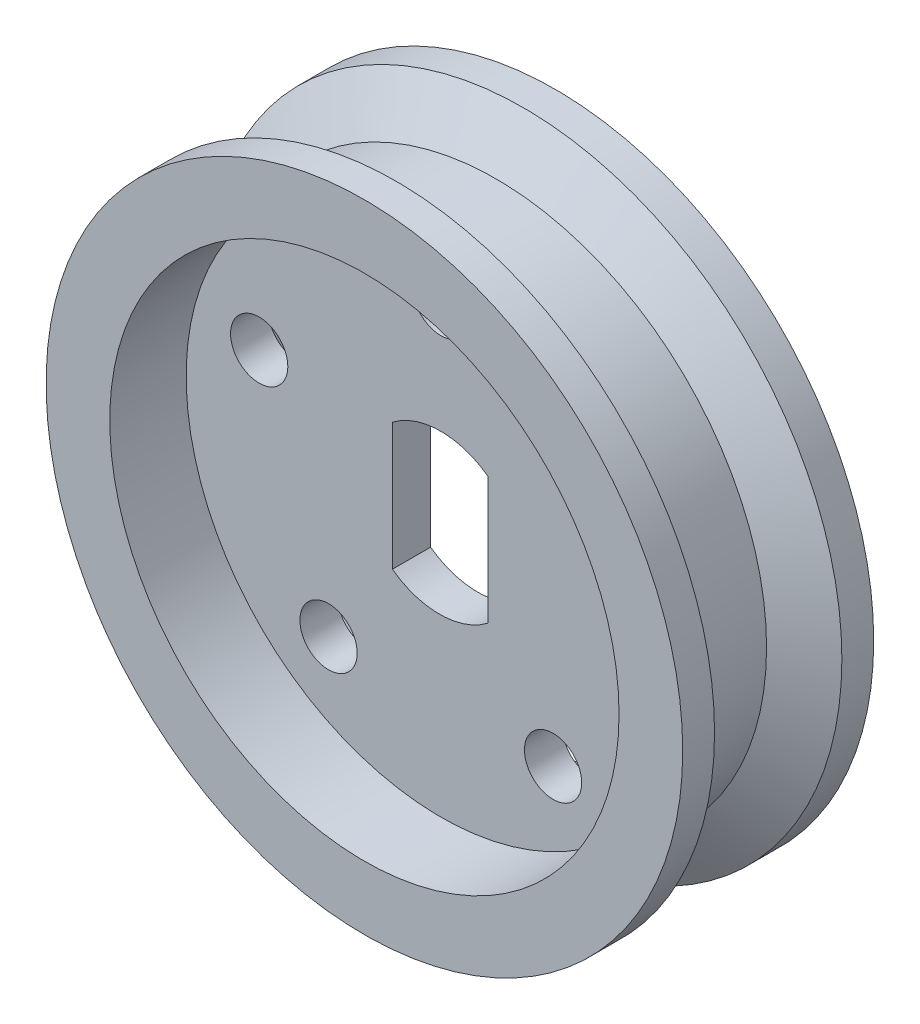
SolidWorks part; units mm, degrees
ref_plane "Front Plane" through (0, 0, 0) normal (0, 0, 1) x (1, 0, 0)
ref_plane "Top Plane" through (0, 0, 0) normal (0, 1, 0) x (1, 0, 0)
ref_plane "Right Plane" through (0, 0, 0) normal (1, 0, 0) x (0, 0, -1)
sketch "Sketch1" plane through (0, 0, 0) normal (0, 0, 1) x (1, 0, 0)
  line L0 (-1.5216, 1.9836) -> (-1.5216, -2.0164)
  line L1 (1.4783, 2.0161) -> (1.4783, -1.9839)
  circle A0 centre (0, 0) radius 10
  arc A2 (-1.5216, 1.9836) -> (1.4783, 2.0161) centre (0, 0) cw
  arc A3 (-1.5216, -2.0164) -> (1.4783, -1.9839) centre (-0.0433, -0.0002) ccw
extrude "Boss-Extrude1" add sketch "Sketch1" along normal mid plane 6
sketch "Sketch2" plane through (0, 0, 3) normal (0, 0, 1) x (1, 0, 0)
  circle A0 centre (0, 0) radius 8
  dimension "D1" = 16
extrude "Cut-Extrude1" cut sketch "Sketch2" against normal blind 2.4
sketch "Sketch3" plane through (0, 0, 0.6) normal (0, 0, 1) x (1, 0, 0)
  circle A0 centre (0, 6) radius 0.9
  circle A1 centre (5.7063, 1.8541) radius 0.9
  circle A2 centre (3.5267, -4.8541) radius 0.9
  circle A3 centre (-3.5267, -4.8541) radius 0.9
  circle A4 centre (-5.7063, 1.8541) radius 0.9
  point P13 (0, 0)
  dimension "D1" = 6
  dimension "D2" = 1.8
  dimension "D3" = 5
ref_plane "Plane1" through (-1.5216, -2.0164, 0.6) normal (0.8065, -0.5913, 0) x (0, 0, -1)
mirror "Mirror1" about plane through (0, 0, 0) normal (0, 0, 1) of "Cut-Extrude1"
sketch "Sketch5" plane through (0, 0, 0) normal (0, 1, 0) x (1, 0, 0)
  line L0 (0, 0) -> (0, 5.2467) construction
  line L1 (-10, 2) -> (-8.5, 1.134)
  line L2 (-10, 3) -> (-10, -3) construction
  line L3 (-8.5, 1.134) -> (-8.5, -1.134)
  line L4 (-8.5, -1.134) -> (-10, -2)
  line L5 (-10, -2) -> (-10, 2)
  point P10 (-10, 0)
  dimension "D1" = 1
  dimension "D2" = 1
  dimension "D3" = 60
  dimension "D4" = 60
  dimension "D5" = 1.5
revolve "Cut-Revolve1" cut sketch "Sketch5" angle 360 about L0
sketch "Sketch6" plane through (0, 0, -0.6) normal (0, 0, -1) x (-1, 0, 0)
  circle A0 centre (0, 0) radius 4.125
  dimension "D1" = 8.25
extrude "Cut-Extrude3" cut sketch "Sketch3" against normal through all contours A3 | A0 | A1 | A2 | A4
